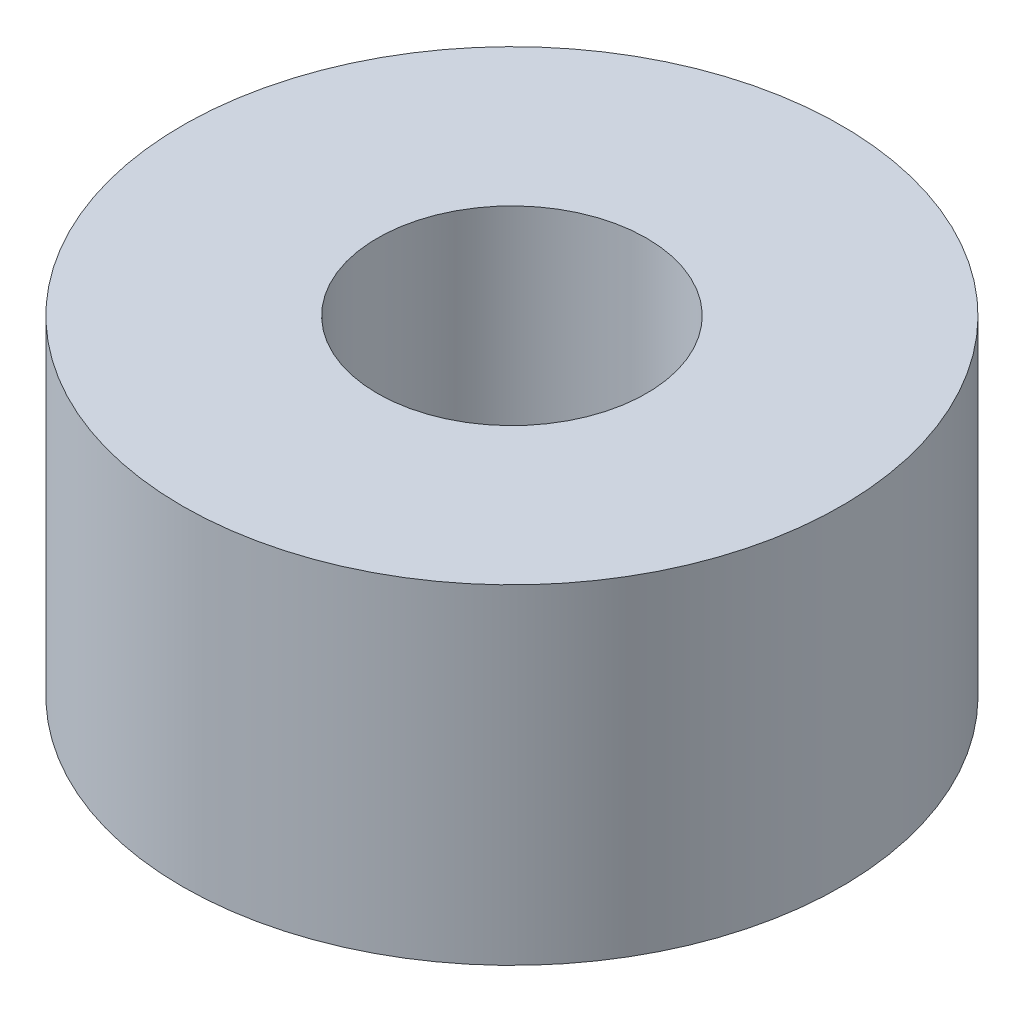
SolidWorks part; units mm, degrees
ref_plane "前视基准面" through (0, 0, 0) normal (0, 0, 1) x (1, 0, 0)
ref_plane "上视基准面" through (0, 0, 0) normal (0, 1, 0) x (1, 0, 0)
ref_plane "右视基准面" through (0, 0, 0) normal (1, 0, 0) x (0, 0, -1)
sketch "草图1" plane through (0, 0, 0) normal (0, 1, 0) x (1, 0, 0)
  line L0 (0, 6.7437) -> (0, -6.8111) construction
  line L1 (-4.5216, 0) -> (7.8641, 0) construction
  circle A0 centre (0, 4.9501) radius 1.05
  circle A1 centre (0, 4.9501) radius 3
  circle A2 centre (0, -4.9501) radius 3
  circle A3 centre (0, -4.9501) radius 1.05
  circle A4 centre (10, -4.9501) radius 3
  circle A5 centre (10, 4.9501) radius 1.075
  circle A6 centre (20, 4.9501) radius 1.225
  circle A7 centre (10, 4.9501) radius 3
  circle A8 centre (20, -4.9501) radius 3
  circle A9 centre (30, 4.9501) radius 1.125
  circle A10 centre (30, -4.9501) radius 1.125
  circle A11 centre (20, 4.9501) radius 3
  circle A12 centre (30, -4.9501) radius 3
  circle A13 centre (20, -4.9501) radius 1.225
  circle A14 centre (10, -4.9501) radius 1.075
  circle A15 centre (30, 4.9501) radius 3
  circle A16 centre (10, 4.9501) radius 1.05 [skipped]
  circle A17 centre (20, 4.9501) radius 1.05 [skipped]
  circle A18 centre (30, 4.9501) radius 1.05 [skipped]
  circle A19 centre (30, -4.9501) radius 1.05 [skipped]
  circle A20 centre (20, -4.9501) radius 1.05 [skipped]
  circle A21 centre (10, -4.9501) radius 1.05 [skipped]
  dimension "D1" = 2.1
  dimension "D2" = 6
  dimension "D4" = 2.15
  dimension "D5" = 2.45
  dimension "D6" = 2.25
  dimension "D3" = 4
extrude "凸台-拉伸1" add sketch "草图1" along normal blind 3 contours A11 A6
